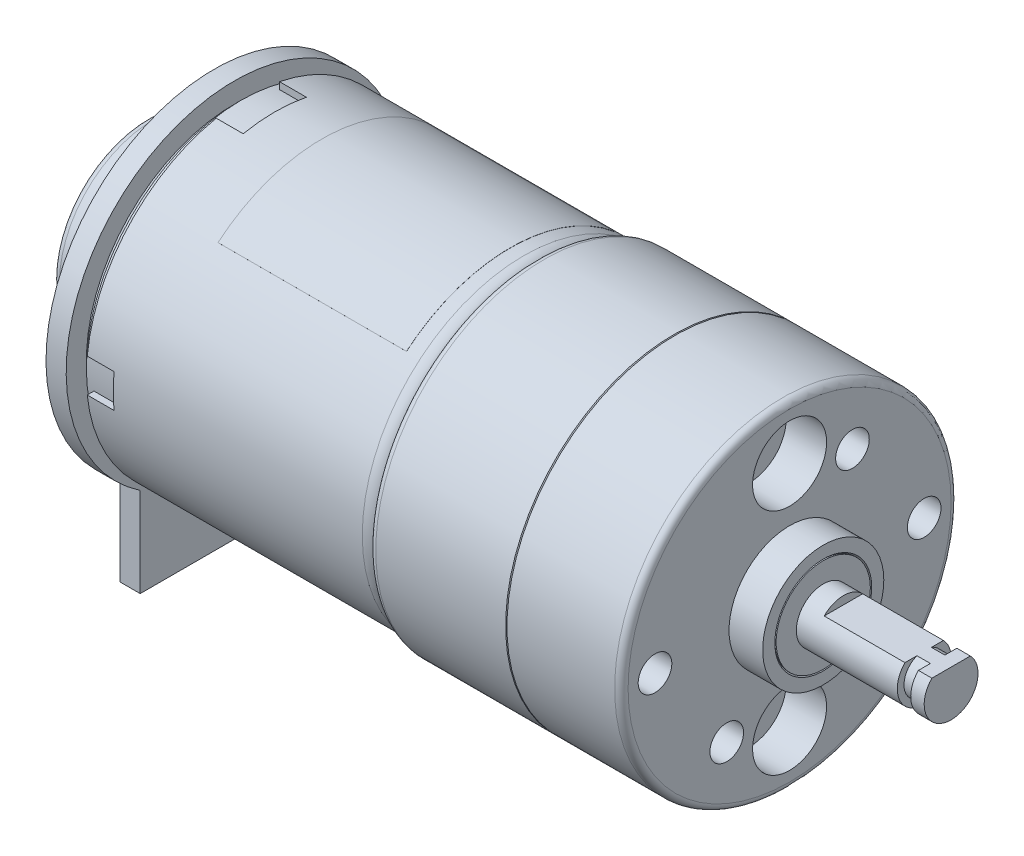
SolidWorks part; units mm, degrees
material "AISI 304"
ref_plane "Plan de face" through (0, 0, 0) normal (0, 0, 1) x (1, 0, 0)
ref_plane "Plan de dessus" through (0, 0, 0) normal (0, 1, 0) x (1, 0, 0)
ref_plane "Plan de droite" through (0, 0, 0) normal (1, 0, 0) x (0, 0, -1)
sketch "Esquisse1" plane through (0, 0, 0) normal (0, 0, 1) x (1, 0, 0)
  line L0 (-41.5667, 0) -> (41.4775, 0) construction
  line L1 (-1, -12) -> (-21.5, -12)
  line L4 (0, 0) -> (0, -11)
  arc A0 (-1, -12) -> (0, -11) centre (-1, -11) ccw
  point P8 (-11.25, -12)
  dimension "D1" = 1
  dimension "D2" = 21.5
  dimension "D3" = 12
revolve "Révol.-Mince3" add sketch "Esquisse1" angle 360 about L0
sketch "Esquisse3" plane through (-21.5, 0, 0) normal (-1, 0, 0) x (0, 0, 1)
  line L0 (0, -13.2934) -> (0, 12.6974) construction
  line L1 (-14.4522, 0) -> (14.2866, 0) construction
  line L2 (-2.35, -10) -> (2.35, -10)
  line L3 (-2.35, -10) -> (-2.35, -13)
  line L4 (-2.35, -13) -> (2.35, -13)
  line L5 (2.35, -10) -> (2.35, -13)
  line L6 (2.35, 10) -> (2.35, 13)
  line L7 (-2.35, 13) -> (2.35, 13)
  line L8 (-2.35, 10) -> (-2.35, 13)
  line L9 (-2.35, 10) -> (2.35, 10)
  line L10 (10, 1.25) -> (10, -1.25)
  line L11 (-13, 1.25) -> (-10, 1.25)
  line L12 (-13, 1.25) -> (-13, -1.25)
  line L13 (-13, -1.25) -> (-10, -1.25)
  line L14 (-10, 1.25) -> (-10, -1.25)
  line L15 (13, 1.25) -> (13, -1.25)
  line L16 (13, -1.25) -> (10, -1.25)
  line L17 (13, 1.25) -> (10, 1.25)
  dimension "D1" = 4.7
  dimension "D2" = 10
  dimension "D3" = 3
  dimension "D4" = 2.5
  dimension "D5" = 10
  dimension "D6" = 3
extrude "Enlèv. mat.-Extru.1" cut sketch "Esquisse3" against normal blind 2
sketch "Esquisse4" plane through (0, 0, 0) normal (0, 0, 1) x (1, 0, 0)
  line L0 (-0.5, 11) -> (-0.5, -11) construction
  line L1 (-0.5, 11) -> (-0.5, 0)
  line L2 (-1, 11.5) -> (-22.5, 11.5)
  line L3 (-25.2684, 0) -> (2.5765, 0) construction
  line L4 (-22.5, 11.5) -> (-22.5, 0)
  line L5 (-22.5, 0) -> (-0.5, 0)
  line L6 (-21.5, 11.7676) -> (-21.5, 1.25) construction
  arc A1 (-0.5, 11) -> (-1, 11.5) centre (-1, 11) ccw construction
  arc A3 (-0.5, 11) -> (-1, 11.5) centre (-1, 11) ccw
  dimension "D1" = 1
revolve "Révolution2" add sketch "Esquisse4" angle 360 about L3
chamfer "Chanfrein1" distance 0.5 angle 45 1 edges at (-22.5, 0, 11.5)
sketch "Esquisse5" plane through (-22.5, 0, 0) normal (-1, 0, 0) x (0, 0, 1)
  line L0 (0, 13.2934) -> (0, -15.7097) construction
  line L2 (-7, -10.3562) -> (-7, -17)
  line L3 (-7, -17) -> (7, -17)
  line L4 (7, -10.3562) -> (7, -17)
  arc A0 (7, -10.3562) -> (-7, -10.3562) centre (0, 0) ccw
  circle A1 centre (0, 0) radius 1.25
  dimension "D1" = 25
  dimension "D4" = 2.5
  dimension "D2" = 17
  dimension "D3" = 14
extrude "Boss.-Extru.1" add sketch "Esquisse5" along normal blind 1.5
sketch "Esquisse6" plane through (0, 0, 0) normal (1, 0, 0) x (0, 0, -1)
  circle A0 centre (0, 0) radius 12.5
  dimension "D1" = 25
extrude "Boss.-Extru.2" add sketch "Esquisse6" along normal blind 10.25
fillet "Congé2" radius 0.5 1 edges at (0, 0, -12.5)
chamfer "Chanfrein2" distance 0.1 angle 45 1 edges at (10.25, 0, -12.5)
sketch "Esquisse7" plane through (10.25, 0, 0) normal (1, 0, 0) x (0, 0, -1)
  circle A0 centre (0, 0) radius 12.5
  dimension "D1" = 25
extrude "Boss.-Extru.3" add sketch "Esquisse7" along normal blind 8.5
fillet "Congé3" radius 0.5 1 edges at (18.75, 0, -12.5)
sketch "Esquisse8" plane through (18.75, 0, 0) normal (1, 0, 0) x (0, 0, -1)
  circle A0 centre (0, 0) radius 4.5
  circle A1 centre (0, 0) radius 3.5
  dimension "D1" = 9
  dimension "D2" = 7
extrude "Boss.-Extru.4" add sketch "Esquisse8" along normal blind 2.5
chamfer "Chanfrein3" distance 0.1 angle 45 1 edges at (21.25, 0, -3.5)
sketch "Esquisse10" plane through (18.75, 0, 0) normal (1, 0, 0) x (0, 0, -1)
  circle A0 centre (0, 0) radius 3.5
  circle A1 centre (0, 0) radius 2
  dimension "D1" = 7
  dimension "D2" = 4
extrude "Boss.-Extru.6" add sketch "Esquisse10" along normal blind 2.5
sketch "Esquisse11" plane through (18.75, 0, 0) normal (1, 0, 0) x (0, 0, -1)
  circle A0 centre (0, 0) radius 2
  dimension "D1" = 4
sketch "Esquisse12" plane through (0, 0, 0) normal (0, 0, 1) x (1, 0, 0)
  line L0 (-4.8722, 0) -> (31.3058, 0) construction
  line L1 (18.75, -2) -> (28.75, -2)
  line L2 (18.75, -2) -> (18.75, 2) construction
  line L3 (18.75, -4.5) -> (18.75, 4.5) construction
  line L4 (28.75, -2) -> (28.75, -1.5)
  line L5 (28.75, -1.5) -> (29.75, -1.5)
  line L6 (29.75, -1.5) -> (29.75, -2)
  line L7 (29.75, -2) -> (30.75, -2)
  line L8 (18.75, -2) -> (18.75, 0)
  line L9 (18.75, 0) -> (30.75, 0)
  line L10 (30.75, 0) -> (30.75, -2)
  dimension "D1" = 4
  dimension "D2" = 12
  dimension "D3" = 1
  dimension "D4" = 1
  dimension "D5" = 1.5
revolve "Révolution3" add sketch "Esquisse12" angle 360 about L0
sketch "Esquisse13" plane through (30.75, 0, 0) normal (1, 0, 0) x (0, 0, -1)
  line L0 (-4.9343, 0) -> (6.9395, 0) construction
  line L2 (-5.2488, 5.489) -> (6.3104, 5.489)
  line L3 (-5.2488, 5.489) -> (-5.2488, 1.4)
  line L4 (-5.2488, 1.4) -> (6.3104, 1.4)
  line L5 (6.3104, 5.489) -> (6.3104, 1.4)
  dimension "D1" = 1.4
extrude "Enlèv. mat.-Extru.2" cut sketch "Esquisse13" against normal blind 8
sketch "Esquisse14" plane through (-22.5, 0, 0) normal (-1, 0, 0) x (0, 0, 1)
  circle A0 centre (0, 0) radius 1
  dimension "D1" = 2
extrude "Boss.-Extru.8" add sketch "Esquisse14" along normal blind 7.5
ref_plane "Plan1" through (-29, 0, 0) normal (-1, 0, 0) x (0, 0, 1)
sketch "Esquisse16" plane through (-29, 0, 0) normal (-1, 0, 0) x (0, 0, 1)
  circle A0 centre (0, 0) radius 7
  circle A1 centre (0, 0) radius 3.5
  dimension "D1" = 14
  dimension "D2" = 7
extrude "Boss.-Extru.9" add sketch "Esquisse16" against normal blind 4 separate body
fillet "Congé4" radius 0.5 2 edges at (-29, 0, 7) (-25, 0, 7)
sketch "Esquisse17" plane through (-29, 0, 0) normal (-1, 0, 0) x (0, 0, 1)
  circle A0 centre (0, 0) radius 3.5
  circle A1 centre (0, 0) radius 1.005
  dimension "D1" = 7
  dimension "D2" = 2.01
extrude "Boss.-Extru.10" add sketch "Esquisse17" against normal blind 4.1 and the other way blind 0.1
sketch "Esquisse18" plane through (18.75, 0, 0) normal (1, 0, 0) x (0, 0, -1)
  line L0 (-14.5069, 0) -> (15.7719, 0) construction
  line L1 (0, 13.9299) -> (0, -19.6541) construction
  circle A0 centre (0, 8.5) radius 2.75
  circle A2 centre (0, -8.5) radius 2.75
  dimension "D1" = 5.5
  dimension "D2" = 8.5
extrude "Enlèv. mat.-Extru.3" cut sketch "Esquisse18" against normal blind 3
hole_wizard "Trou taraudé M31" positions "Esquisse20" profile "Esquisse19" tap size "M3" standard "ISO"
sketch "Esquisse20" plane through (18.75, 0, 0) normal (1, 0, 0) x (0, 0, -1)
  line L0 (-15.2822, 0) -> (14.9557, 0) construction
  point P0 (-10, 0)
  dimension "D1" = 10
sketch "Esquisse19" plane through (18.75, 0, 10) normal (0, 1, 0) x (0, 0, -1)
  line L0 (0, 0) -> (0, 9.2511)
  line L1 (0, 9.2511) -> (1.25, 8.5)
  line L2 (1.25, 8.5) -> (1.25, 0)
  line L5 (1.25, 0) -> (0, 0)
  line L10 (0, 9.2511) -> (-1.25, 8.5) construction
  line L11 (0, -6.35) -> (0, 107.95) construction
  dimension "Diamètre du trou pour taraudage" = 2.5
  dimension "Profondeur du trou pour taraudage" = 8.5
  dimension "Angle de pointe" = 118
cosmetic thread "Filetage de perçage1" parameters "D1"=6, "D2"=3
mirror "Symétrie1" about plane through (0, 0, 0) normal (0, 0, 1) of "Trou taraudé M31"
hole_wizard "Trou taraudé M32" positions "Esquisse23" profile "Esquisse24" tap size "M3" standard "ISO"
sketch "Esquisse23" plane through (18.75, 0, 0) normal (1, 0, 0) x (0, 0, -1)
  line L0 (-4.6704, -7.1019) -> (4.6704, 7.1019) construction
  line L1 (0, 0) -> (0, 13.9299) construction
  point P0 (4.6704, 7.1019)
  point P2 (-4.6704, -7.1019)
  dimension "D1" = 17
  dimension "D2" = 33.33
sketch "Esquisse24" plane through (18.75, 7.1019, -4.6704) normal (0, 1, 0) x (0, 0, -1)
  line L0 (0, 0) -> (0, 9.2511)
  line L1 (0, 9.2511) -> (1.25, 8.5)
  line L2 (1.25, 8.5) -> (1.25, 0)
  line L5 (1.25, 0) -> (0, 0)
  line L10 (0, 9.2511) -> (-1.25, 8.5) construction
  line L11 (0, -6.35) -> (0, 107.95) construction
  dimension "Diamètre du trou pour taraudage" = 2.5
  dimension "Profondeur du trou pour taraudage" = 8.5
  dimension "Angle de pointe" = 118
cosmetic thread "Filetage de perçage2" parameters "D1"=6, "D2"=3
cosmetic thread "Filetage de perçage3" parameters "D1"=6, "D2"=3
ref_plane "Plan2" through (-2, 0, 0) normal (1, 0, 0) x (0, 0, -1)
sketch "Esquisse25" plane through (-2, 0, 0) normal (1, 0, 0) x (0, 0, -1)
  line L0 (0, 0) -> (0, 14.1001) construction
  line L1 (-7.7135, 9.1925) -> (0, 0) construction
  line L2 (7.7135, 9.1925) -> (7.7199, 9.2002)
  line L3 (-7.7199, 9.2002) -> (-7.7135, 9.1925)
  arc A0 (7.7135, 9.1925) -> (-7.7135, 9.1925) centre (0, 0) ccw
  arc A1 (7.7199, 9.2002) -> (-7.7199, 9.2002) centre (0, 0) ccw
  dimension "D2" = 12
  dimension "D1" = 40
  dimension "D3" = 0.01
extrude "Boss.-Extru.11" add sketch "Esquisse25" against normal blind 14
